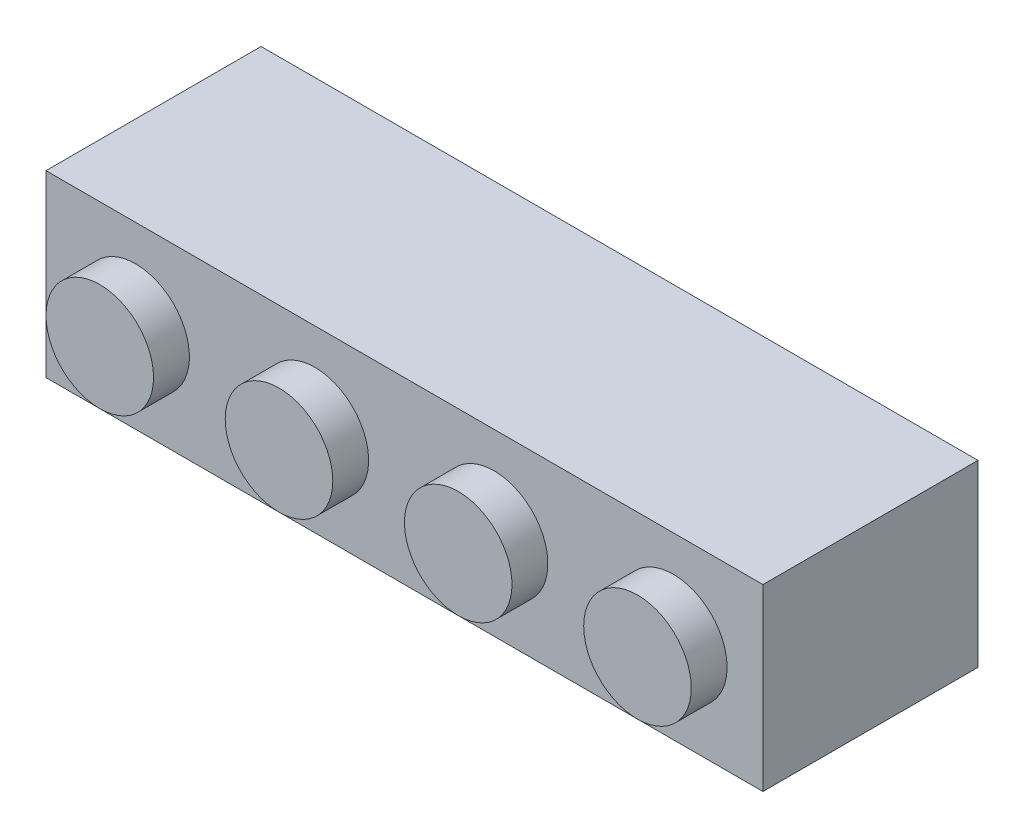
SolidWorks part; units mm, degrees
ref_plane "Front Plane" through (0, 0, 0) normal (0, 0, 1) x (1, 0, 0)
ref_plane "Top Plane" through (0, 0, 0) normal (0, 1, 0) x (1, 0, 0)
ref_plane "Right Plane" through (0, 0, 0) normal (1, 0, 0) x (0, 0, -1)
sketch "Sketch1" plane through (0, 0, 0) normal (0, 0, 1) x (1, 0, 0)
  line L1 (0, 0) -> (32, 0)
  line L2 (0, 0) -> (0, 8)
  line L3 (0, 8) -> (32, 8)
  line L4 (32, 0) -> (32, 8)
  dimension "D1" = 8
  dimension "D2" = 32
extrude "Boss-Extrude1" add sketch "Sketch1" along normal blind 9.6
sketch "Sketch2" plane through (0, 0, 9.6) normal (0, 0, 1) x (1, 0, 0)
  line L1 (32, 8) -> (0, 8) construction
  line L2 (0, 8) -> (0, 0) construction
  circle A0 centre (4, 4) radius 2.4
  dimension "D1" = 4.8
  dimension "D2" = 1.6
  dimension "D3" = 1.6
extrude "Boss-Extrude2" add sketch "Sketch2" along normal blind 1.6
pattern_linear "LPattern1" count 4 spacing 8 along (1, 0, 0) of "Boss-Extrude2"
shell "Shell1" thickness 1.6
sketch "Sketch3" plane through (0, 0, 8) normal (0, 0, -1) x (-1, 0, 0)
  line L0 (0, 0) -> (-32, 0) construction
  line L1 (0, 8) -> (0, 0) construction
  circle A0 centre (-8, 4) radius 1.6
  dimension "D1" = 3.2
  dimension "D2" = 4
  dimension "D3" = 8
extrude "Boss-Extrude3" add sketch "Sketch3" along normal blind 8 contours A0
pattern_linear "LPattern2" count 3 spacing 8 along (1, 0, 0) of "Boss-Extrude3"
